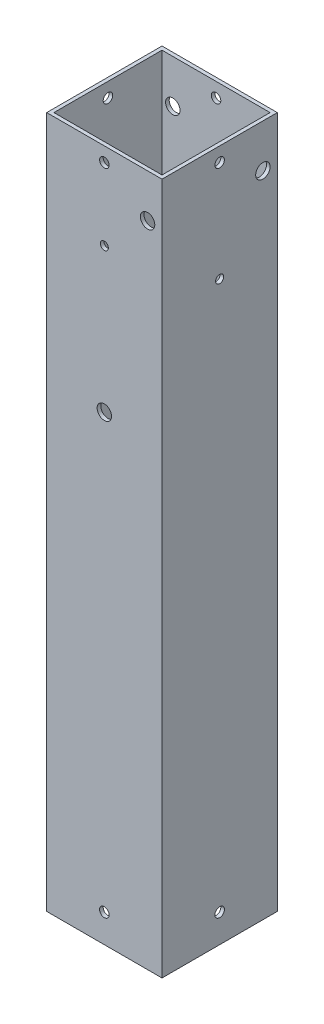
SolidWorks part; units mm, degrees
material "6061 Alloy"
ref_plane "Front Plane" through (0, 0, 0) normal (0, 0, 1) x (1, 0, 0)
ref_plane "Top Plane" through (0, 0, 0) normal (0, 1, 0) x (1, 0, 0)
ref_plane "Right Plane" through (0, 0, 0) normal (1, 0, 0) x (0, 0, -1)
sketch "Sketch1" plane through (0, 0, 0) normal (0, 1, 0) x (1, 0, 0)
  line L1 (-23.8125, 23.8125) -> (23.8125, 23.8125)
  line L2 (-23.8125, 23.8125) -> (-23.8125, -23.8125)
  line L3 (-23.8125, -23.8125) -> (23.8125, -23.8125)
  line L4 (23.8125, 23.8125) -> (23.8125, -23.8125)
  line L5 (-25.4, 25.4) -> (25.4, 25.4)
  line L6 (-25.4, 25.4) -> (-25.4, -25.4)
  line L7 (-25.4, -25.4) -> (25.4, -25.4)
  line L8 (25.4, 25.4) -> (25.4, -25.4)
  point P2 (-25.4, 0)
  point P11 (-23.8125, 0)
  point P12 (0, 23.8125)
  point P13 (0, 25.4)
  dimension "D1" = 47.625
  dimension "1.95" = 47.625
  dimension "2.05" = 50.8
  dimension "D2" = 50.8
extrude "Boss-Extrude1" add sketch "Sketch1" along normal blind 304.8
ref_plane "Plane1" [suppressed] through (0, 152.4, 0) normal (0, 1, 0) x (1, 0, 0)
sketch "Sketch6" plane through (25.4, 0, 0) normal (1, 0, 0) x (0, 0, -1)
  line L0 (-25.4, 0) -> (25.4, 0) construction
  line L1 (25.4, 304.8) -> (25.4, 0) construction
  circle A0 centre (0, 12.4124) radius 2.0955
  dimension "D1" = 12.4124
  dimension "D2" = 4.191
  dimension "D3" = 25.4
extrude "Cut-Extrude3" cut sketch "Sketch6" against normal through all both and the other way through all
sketch "Sketch7" plane through (0, 0, -25.4) normal (0, 0, -1) x (-1, 0, 0)
  line L0 (-25.4, 0) -> (25.4, 0) construction
  circle A0 centre (0, 12.4124) radius 2.0955
  dimension "D1" = 4.191
  dimension "D2" = 12.4124
  dimension "D3" = 25.4
extrude "Cut-Extrude4" cut sketch "Sketch7" against normal through all both
sketch "Sketch8" plane through (25.4, 0, 0) normal (1, 0, 0) x (0, 0, -1)
  line L0 (-25.4, 304.8) -> (25.4, 304.8) construction
  line L1 (-25.4, 304.8) -> (-25.4, 0) construction
  circle A0 centre (0, 298.45) radius 2.0955
  dimension "D1" = 4.191
  dimension "D2" = 6.35
  dimension "D3" = 25.4
extrude "Cut-Extrude5" cut sketch "Sketch8" against normal through all
sketch "Sketch9" plane through (0, 0, 25.4) normal (0, 0, 1) x (1, 0, 0)
  line L0 (-25.4, 304.8) -> (-25.4, 0) construction
  line L1 (-25.4, 304.8) -> (25.4, 304.8) construction
  circle A0 centre (0, 298.45) radius 2.0955
  dimension "D1" = 4.191
  dimension "D2" = 25.4
  dimension "D3" = 6.35
extrude "Cut-Extrude6" cut sketch "Sketch9" against normal through all
sketch "Sketch10" plane through (0, 0, 25.4) normal (0, 0, 1) x (1, 0, 0)
  line L0 (25.4, 304.8) -> (25.4, 0) construction
  line L1 (-25.4, 304.8) -> (25.4, 304.8) construction
  circle A0 centre (19.05, 285.75) radius 3.175
  dimension "D1" = 6.35
  dimension "D2" = 6.35
  dimension "D3" = 19.05
extrude "Cut-Extrude7" cut sketch "Sketch10" against normal blind 5.08
sketch "Sketch11" plane through (-25.4, 0, 0) normal (-1, 0, 0) x (0, 0, 1)
  line L0 (25.4, 304.8) -> (25.4, 0) construction
  line L1 (-25.4, 304.8) -> (25.4, 304.8) construction
  circle A0 centre (19.05, 285.75) radius 3.175
  dimension "D1" = 6.35
  dimension "D2" = 6.35
  dimension "D3" = 19.05
extrude "Cut-Extrude8" cut sketch "Sketch11" against normal blind 5.08
sketch "Sketch12" plane through (0, 0, -25.4) normal (0, 0, -1) x (-1, 0, 0)
  line L0 (25.4, 304.8) -> (25.4, 0) construction
  line L1 (-25.4, 304.8) -> (25.4, 304.8) construction
  circle A0 centre (19.05, 285.75) radius 3.175
  dimension "D1" = 6.35
  dimension "D2" = 6.35
  dimension "D3" = 19.05
extrude "Cut-Extrude9" cut sketch "Sketch12" against normal blind 5.08
sketch "Sketch13" plane through (25.4, 0, 0) normal (1, 0, 0) x (0, 0, -1)
  line L0 (-25.4, 304.8) -> (25.4, 304.8) construction
  line L1 (25.4, 304.8) -> (25.4, 0) construction
  circle A0 centre (19.05, 285.75) radius 3.175
  dimension "D1" = 6.35
  dimension "D2" = 19.05
  dimension "D3" = 6.35
extrude "Cut-Extrude10" cut sketch "Sketch13" against normal blind 5.08
sketch "Sketch15" plane through (0, 0, -25.4) normal (0, 0, -1) x (-1, 0, 0)
  line L0 (-25.4, 304.8) -> (25.4, 304.8) construction
  circle A0 centre (0, 222.25) radius 1.778
  circle A1 centre (0, 190.5) radius 3.175
  dimension "D1" = 3.556
  dimension "D3" = 114.3
  dimension "D4" = 6.35
  dimension "D2" = 82.55
extrude "Cut-Extrude12" cut sketch "Sketch15" against normal blind 5.08
sketch "Sketch16" plane through (25.4, 0, 0) normal (1, 0, 0) x (0, 0, -1)
  line L0 (-25.4, 304.8) -> (25.4, 304.8) construction
  circle A0 centre (0, 254) radius 1.778
  dimension "D1" = 3.556
  dimension "D2" = 50.8
extrude "Cut-Extrude13" cut sketch "Sketch16" against normal blind 5.08
sketch "Sketch17" plane through (-25.4, 0, 0) normal (-1, 0, 0) x (0, 0, 1)
  line L0 (-25.4, 304.8) -> (25.4, 304.8) construction
  circle A0 centre (0, 203.2) radius 1.778
  dimension "D1" = 3.556
  dimension "D2" = 101.6
extrude "Cut-Extrude14" cut sketch "Sketch17" against normal blind 5.08
sketch "Sketch19" plane through (0, 0, 25.4) normal (0, 0, 1) x (1, 0, 0)
  line L0 (-25.4, 304.8) -> (25.4, 304.8) construction
  circle A0 centre (0, 266.7) radius 1.778
  circle A1 centre (0, 203.2) radius 3.175
  dimension "D1" = 6.35
  dimension "D2" = 3.556
  dimension "D3" = 38.1
  dimension "D4" = 101.6
extrude "Cut-Extrude15" cut sketch "Sketch19" against normal blind 5.08
equation "\"1.95@Sketch1\"=2-(1/8)"
equation "\"D1@Sketch1\"=\"1.95@Sketch1\""
